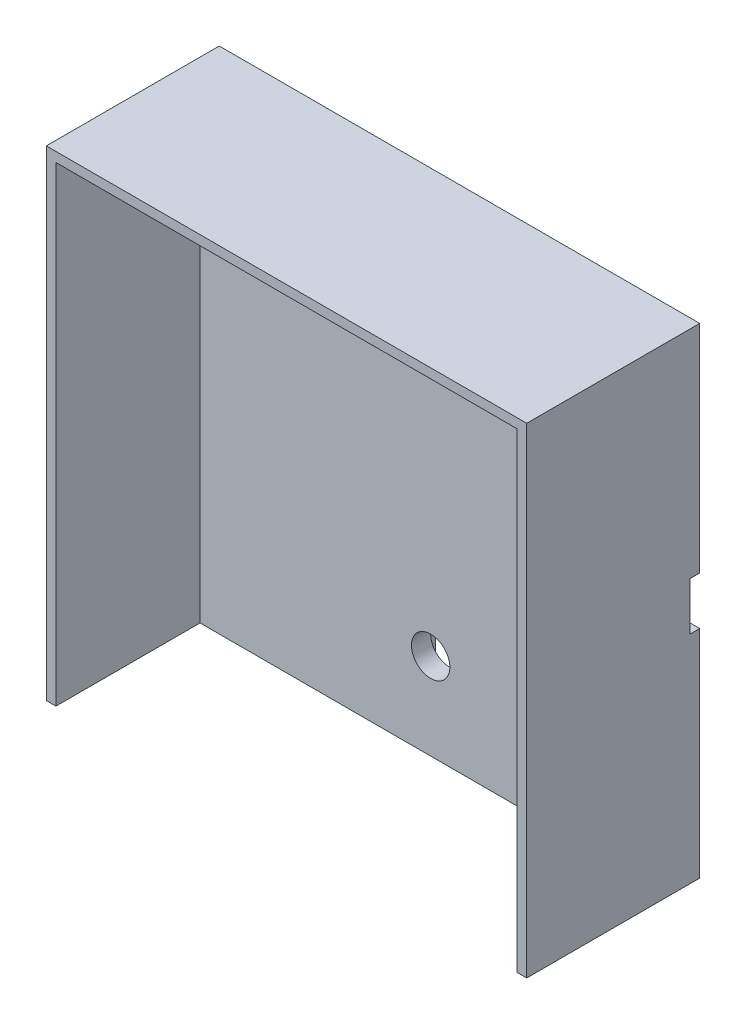
SolidWorks part; units mm, degrees
ref_plane "Přední rovina" through (0, 0, 0) normal (0, 0, 1) x (1, 0, 0)
ref_plane "Horní rovina" through (0, 0, 0) normal (0, 1, 0) x (1, 0, 0)
ref_plane "Pravá rovina" through (0, 0, 0) normal (1, 0, 0) x (0, 0, -1)
sketch "Skica1" plane through (0, 0, 0) normal (0, 0, 1) x (1, 0, 0)
  line L1 (25, 25) -> (-25, 25)
  line L2 (25, 25) -> (25, -25)
  line L3 (25, -25) -> (-25, -25)
  line L4 (-25, 25) -> (-25, -25)
  line L5 (25, 25) -> (-25, -25) construction
  line L6 (25, -25) -> (-25, 25) construction
  point P0 (0, 0)
  point P5 (-27.5, 0)
  point P11 (4.5, 0)
  dimension "D1" = 50
  dimension "D2" = 50
extrude "Přidat vysunutím2" add sketch "Skica1" along normal blind 3 contours L2 L1 L4 L3
sketch "Skica5" plane through (0, 0, 0) normal (0, 0, -1) x (-1, 0, 0)
  line L0 (-25, 25) -> (-25, -25) construction
  line L5 (-2.5, -2.5) -> (2.5, -2.5)
  line L15 (-25, -2.5) -> (2.5, -2.5)
  line L16 (-25, -2.5) -> (-25, 2.5)
  line L17 (-2.5, -2.5) -> (-2.5, -25)
  line L18 (-2.5, -25) -> (2.5, -25)
  line L19 (2.5, -2.5) -> (2.5, -25)
  line L20 (-2.5, -2.5) -> (2.5, -25) construction
  line L21 (-2.5, -25) -> (2.5, -2.5) construction
  line L22 (-25, 2.5) -> (2.5, 2.5)
  line L23 (2.5, -2.5) -> (2.5, 2.5)
  point P0 (0, 0)
  point P6 (0, -13.75)
  dimension "D1" = 5
  dimension "D2" = 22.5
  dimension "D3" = 5
extrude "Odebrat vysunutím3" cut sketch "Skica5" against normal blind 1 contours L23 L15 L16 L22 | L17 L5 L19 L18
sketch "Skica14" plane through (0, 0, 3) normal (0, 0, 1) x (1, 0, 0)
  line L1 (-25, 25) -> (25, 25)
  line L2 (-25, 25) -> (-25, -25)
  line L3 (-25, -25) -> (25, -25)
  line L4 (25, 25) -> (25, -25)
  line L5 (-24, 24) -> (24, 24)
  line L6 (-24, 24) -> (-24, -25)
  line L7 (-24, -25) -> (24, -25)
  line L8 (24, 24) -> (24, -25)
  line M13 (-25, -25) -> (25, -25)
  line M14 (25, -25) -> (25, 25)
  line M15 (25, 25) -> (-25, 25)
  line M16 (-25, 25) -> (-25, -25)
  dimension "D1" = 1
  dimension "D2" = 1
  dimension "D3" = 1
  dimension "D4" = 0
extrude "Přidat vysunutím9" add sketch "Skica14" along normal blind 15 contours L5 L8 L6 M13 M14 M15 M16
sketch "Skica17" plane through (0, 0, 1) normal (0, 0, -1) x (-1, 0, 0)
  line L0 (-25, 2.5) -> (-25, -2.5) construction
  line L1 (-10, -2.5) -> (-10, 2.5) construction
  line L3 (-2.5, -25) -> (2.5, -25) construction
  circle A0 centre (-16, 0) radius 2
  circle A2 centre (0, -16) radius 2
  dimension "D1" = 4
  dimension "D6" = 4
  dimension "D3" = 9
  dimension "D4" = 6
  dimension "D7" = 9
extrude "Odebrat vysunutím8" cut sketch "Skica17" against normal blind 4
fillet "Zaoblit1" radius 10 1 edges at (-2.5, 2.5, 0.5)
fillet "Zaoblit2" radius 5 1 edges at (2.5, -2.5, 0.5)
